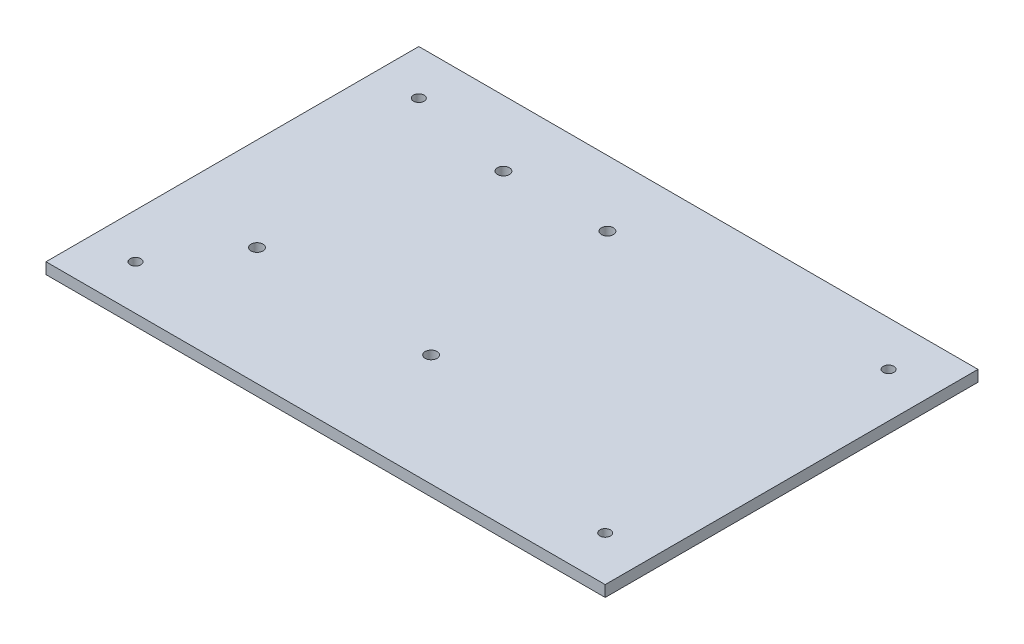
SolidWorks part; units mm, degrees
ref_plane "Front Plane" through (0, 0, 0) normal (0, 0, 1) x (1, 0, 0)
ref_plane "Top Plane" through (0, 0, 0) normal (0, 1, 0) x (1, 0, 0)
ref_plane "Right Plane" through (0, 0, 0) normal (1, 0, 0) x (0, 0, -1)
sketch "Sketch1" plane through (0, 0, 0) normal (0, 1, 0) x (1, 0, 0)
  line L1 (75, -50) -> (-75, -50)
  line L2 (75, -50) -> (75, 50)
  line L3 (75, 50) -> (-75, 50)
  line L4 (-75, -50) -> (-75, 50)
  line L5 (75, -50) -> (-75, 50) construction
  line L6 (75, 50) -> (-75, -50) construction
  point P0 (0, 0)
  dimension "D1" = 150
  dimension "D2" = 100
extrude "Boss-Extrude1" add sketch "Sketch1" along normal blind 3
sketch "Sketch2" plane through (0, 3, 0) normal (0, 1, 0) x (1, 0, 0)
  line L0 (0, 0) -> (-122.3191, 0) construction
  line L1 (-122.3191, 0) -> (115.1579, 0) construction
  line L2 (0, 73.5477) -> (0, -98.9538) construction
  line L3 (75, 50) -> (-75, 50) construction
  line L4 (-75, 50) -> (-75, -50) construction
  circle A0 centre (-63, 38) radius 1.425
  dimension "D1" = 2.85
  dimension "D2" = 12
  dimension "D3" = 12
extrude "Cut-Extrude1" cut sketch "Sketch2" against normal blind 10
pattern_linear "LPattern1" count 1 spacing 126 along (-1, 0, 0) count 2 spacing 76 along (0, 0, 1) of "Cut-Extrude1"
sketch "Sketch3" [suppressed] plane through (0, 3, 0) normal (0, 1, 0) x (1, 0, 0)
  line L0 (47, 37) -> (-47, 37) construction
  line L1 (-47, 37) -> (-47, -37) construction
  circle A0 centre (-38, 28) radius 1.425
  dimension "D1" = 2.85
  dimension "D2" = 9
  dimension "D3" = 9
extrude "Cut-Extrude2" [suppressed] cut sketch "Sketch3" against normal blind 10
pattern_linear "LPattern2" [suppressed] count 2 spacing 76 count 2 spacing 56
sketch "Sketch4" [suppressed] plane through (0, 3, 0) normal (0, 1, 0) x (1, 0, 0)
  line L0 (75, 37) -> (-75, 37) construction
  line L1 (-75, 37) -> (-75, -37) construction
  circle A0 centre (-63, 28) radius 1.425
  dimension "D1" = 2.85
  dimension "D2" = 9
  dimension "D3" = 12
extrude "Cut-Extrude3" [suppressed] cut sketch "Sketch4" against normal blind 10
pattern_linear "LPattern3" [suppressed] count 2 spacing 126 count 2 spacing 56
sketch "Sketch5" plane through (0, 3, 0) normal (0, 1, 0) x (1, 0, 0)
  line L0 (-75, 50) -> (-75, -50) construction
  line L1 (-75, -50) -> (75, -50) construction
  line L3 (-1.7, -20) -> (-81.1724, -20) construction
  line L4 (-6.8, 32.4) -> (-34.7, 32.4) construction
  circle A0 centre (-34.7, 32.4) radius 1.6
  circle A1 centre (-6.8, 32.4) radius 1.6
  circle A2 centre (-1.7, -20) radius 1.6
  circle A4 centre (-50, -18.4) radius 1.6
  dimension "D1" = 3.2
  dimension "D2" = 27.9
  dimension "D3" = 5.1
  dimension "D4" = 50.8
  dimension "D5" = 48.3
  dimension "D6" = 25
  dimension "D7" = 30
extrude "Cut-Extrude4" cut sketch "Sketch5" against normal blind 10
sketch "Sketch6" plane through (0, 0, 0) normal (0, -1, 0) x (1, 0, 0)
  line L0 (-63, 38) -> (100.028, 38) construction
  line L1 (75, 50) -> (75, -50) construction
  line L2 (63, 38) -> (63, -100.5192) construction
  line L3 (-63, -38) -> (102.189, -38) construction
  circle A0 centre (63, 38) radius 1.425
  circle A3 centre (63, -38) radius 1.425
  dimension "D2" = 2.85
  dimension "D1" = 12
extrude "Cut-Extrude5" cut sketch "Sketch6" against normal blind 10
sketch "Sketch10" [suppressed] plane through (0, 3, 0) normal (0, 1, 0) x (1, 0, 0)
  line L0 (-64.9209, 12) -> (65.1586, 12) construction
  line L1 (0, 45.5263) -> (0, -61.4392) construction
  line L2 (75, 37) -> (-75, 37) construction
  circle A0 centre (-39, 12) radius 3.625
  circle A1 centre (-13, 12) radius 3.625
  circle A2 centre (13, 12) radius 3.625
  circle A3 centre (39, 12) radius 3.625
  dimension "D1" = 7.25
  dimension "D2" = 13
  dimension "D3" = 26
  dimension "D4" = 25
extrude "Cut-Extrude8" [suppressed] cut sketch "Sketch10" against normal blind 10
sketch "Sketch11" [suppressed] plane through (0, 0, 0) normal (0, -1, 0) x (1, 0, 0)
  line L0 (-126.9736, 0) -> (96.4357, 0) construction
  line L1 (-34.8, 0) -> (-34.8, 5.5) construction
  line L2 (-35.6, 0) -> (-35.6, 5.5)
  line L3 (-34, 0) -> (-34, 5.5)
  line L4 (0, 50.3887) -> (0, -44.5353) construction
  arc A0 (-38.9163, 4.0147) -> (-30.4291, 3.7359) centre (-34.8, 0) ccw construction
  arc A1 (-39.4533, 4.5384) -> (-29.8589, 4.2232) centre (-34.8, 0) ccw
  arc A2 (-38.3794, 3.4911) -> (-30.9992, 3.2487) centre (-34.8, 0) ccw
  arc A3 (-38.3794, 3.4911) -> (-39.4533, 4.5384) centre (-38.9163, 4.0147) ccw
  arc A4 (-29.8589, 4.2232) -> (-30.9992, 3.2487) centre (-30.4291, 3.7359) ccw
  arc A5 (-35.6, 0) -> (-34, 0) centre (-34.8, 0) ccw
  arc A6 (-34, 5.5) -> (-35.6, 5.5) centre (-34.8, 5.5) ccw
  point P6 (-34.9888, -5.7469)
  point P13 (-34.8, 2.75)
  point P20 (-30.9163, 4.3061)
  dimension "D1" = 6.5
  dimension "D3" = 0.8
  dimension "D5" = 5
  dimension "D7" = 5.7469
  dimension "D2" = 5.5
  dimension "D4" = 8
  dimension "D6" = 34
extrude "Cut-Extrude9" [suppressed] cut sketch "Sketch11" against normal blind 10
sketch "Sketch12" [suppressed] plane through (0, 0, 0) normal (0, -1, 0) x (1, 0, 0)
  line L0 (-84.8642, 0) -> (86.8315, 0) construction
  circle A0 centre (-15, 0) radius 4
  dimension "D1" = 8
  dimension "D2" = 15
extrude "Cut-Extrude10" [suppressed] cut sketch "Sketch12" against normal blind 10
pattern_linear "LPattern4" [suppressed] count 2 spacing 20
sketch "Sketch13" [suppressed] plane through (0, 3, 0) normal (0, 1, 0) x (1, 0, 0)
  line L0 (97.8196, 0) -> (-126.0628, 0) construction
  circle A0 centre (18.87, 0) radius 1.25
  circle A1 centre (-8.38, 0) radius 1.25
  dimension "D1" = 2.5
  dimension "D2" = 27.25
extrude "Cut-Extrude11" [suppressed] cut sketch "Sketch13" against normal blind 10
sketch "Sketch15" [suppressed] plane through (0, 3, 0) normal (0, 1, 0) x (1, 0, 0)
  line L0 (0, -17.7932) -> (0, 22.7245) construction
  line L1 (-22.619, 0) -> (26.3, 0) construction
  line L3 (17.07, -7) -> (-6.58, -7)
  line L4 (17.07, -7) -> (17.07, 7)
  line L5 (17.07, 7) -> (-6.58, 7)
  line L6 (-6.58, -7) -> (-6.58, 7)
  circle A0 centre (18.87, 0) radius 1.25 construction
  circle A1 centre (-8.38, 0) radius 1.25 construction
  dimension "D1" = 1.8
  dimension "D2" = 1.8
  dimension "D3" = 14
extrude "Cut-Extrude12" [suppressed] cut sketch "Sketch15" against normal blind 10
sketch "Sketch16" [suppressed] plane through (0, 3, 0) normal (0, 1, 0) x (1, 0, 0)
  line L5 (-75, 37) -> (-75, -37) construction
  line L6 (-44.5, -11.5) -> (-30.5, -11.5)
  line L7 (-44.5, -11.5) -> (-44.5, -23.5)
  line L8 (-44.5, -23.5) -> (-30.5, -23.5)
  line L9 (-30.5, -11.5) -> (-30.5, -23.5)
  line L10 (-75, -37) -> (75, -37) construction
  dimension "D1" = 14
  dimension "D2" = 30.5
  dimension "D3" = 25.5
  dimension "D4" = 12
extrude "Cut-Extrude13" [suppressed] cut sketch "Sketch16" against normal blind 10
sketch "Sketch17" [suppressed] plane through (0, -77, 0) normal (0, -1, 0) x (1, 0, 0)
  line L0 (-83.0645, 0) -> (81.9128, 0) construction
  line L1 (-50, -30) -> (-15, -30)
  line L2 (-50, -30) -> (-50, 30)
  line L3 (-50, 30) -> (-15, 30)
  line L4 (-15, -30) -> (-15, 30)
  dimension "D1" = 35
  dimension "D2" = 60
  dimension "D3" = 15
extrude "Cut-Extrude15" [suppressed] cut sketch "Sketch17" against normal through all
